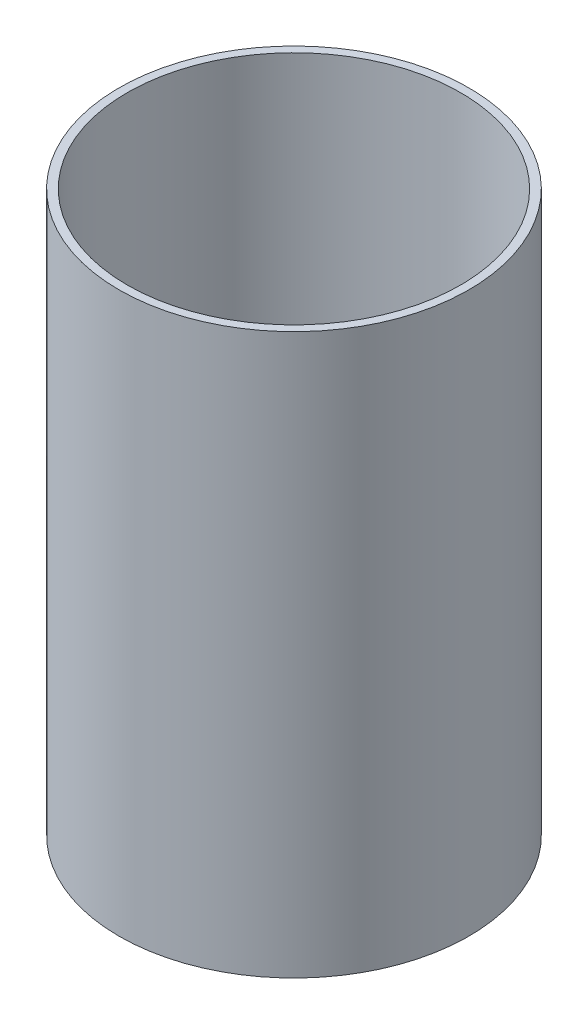
SolidWorks part; units mm, degrees
material "C-Glass Fiber"
ref_plane "Front Plane" through (0, 0, 0) normal (0, 0, 1) x (1, 0, 0)
ref_plane "Top Plane" through (0, 0, 0) normal (0, 1, 0) x (1, 0, 0)
ref_plane "Right Plane" through (0, 0, 0) normal (1, 0, 0) x (0, 0, -1)
sketch "Sketch1" plane through (0, 0, 0) normal (0, 1, 0) x (1, 0, 0)
  circle A0 centre (0, 0) radius 60.5028
  circle A1 centre (0, 0) radius 63.5
  dimension "D1" = 127
  dimension "D2" = 121.0056
extrude "Boss-Extrude1" add sketch "Sketch1" along normal blind 203.2
